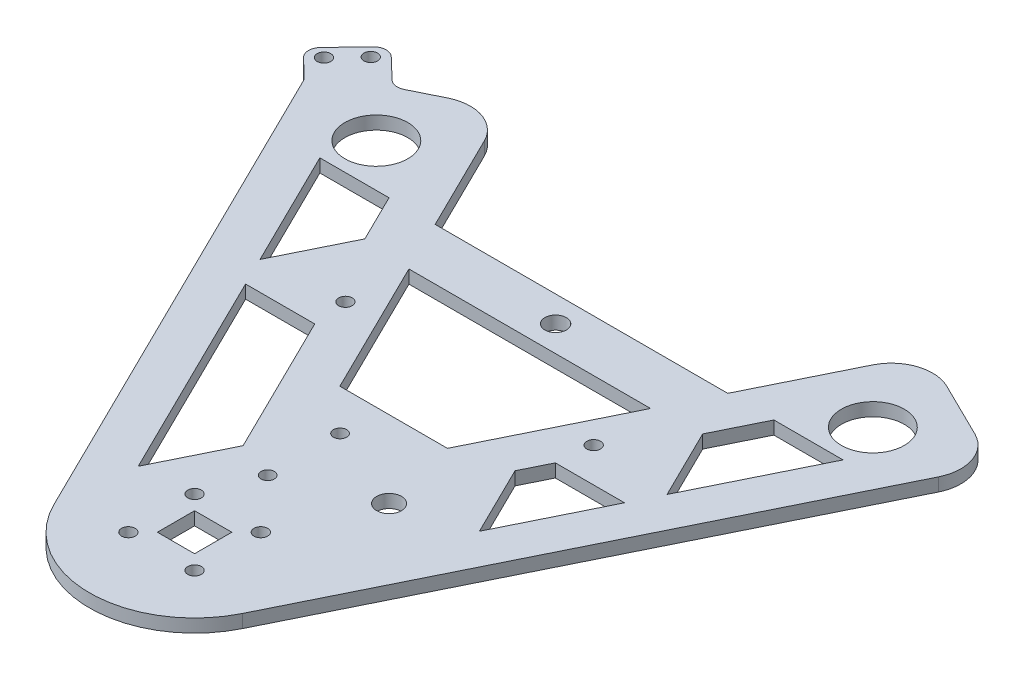
SolidWorks part; units mm, degrees
ref_plane "Front Plane" through (0, 0, 0) normal (0, 0, 1) x (1, 0, 0)
ref_plane "Top Plane" through (0, 0, 0) normal (0, 1, 0) x (1, 0, 0)
ref_plane "Right Plane" through (0, 0, 0) normal (1, 0, 0) x (0, 0, -1)
sketch "Sketch1" plane through (0, 0, 0) normal (0, 1, 0) x (1, 0, 0)
  line L0 (-60, 103.923) -> (60, 103.923) construction
  line L1 (-4.5, -4.5) -> (4.5, -4.5)
  line L2 (-4.5, -4.5) -> (-4.5, 4.5)
  line L3 (-4.5, 4.5) -> (4.5, 4.5)
  line L4 (4.5, -4.5) -> (4.5, 4.5)
  line L5 (-4.5, -4.5) -> (4.5, 4.5) construction
  line L6 (-4.5, 4.5) -> (4.5, -4.5) construction
  line L7 (-82.7138, 110.4306) -> (-22.7854, -11.2243)
  line L8 (22.7854, -11.2243) -> (82.7138, 110.4306)
  line L9 (-51.3166, 125.8972) -> (0, 21.7243)
  line L10 (0, 21.7243) -> (51.3166, 125.8972)
  line L11 (51.3166, 125.8972) -> (82.7138, 110.4306)
  line L12 (-82.7138, 110.4306) -> (-51.3166, 125.8972)
  line L13 (-57.5832, 99.017) -> (-36.1852, 55.5789) construction
  line L14 (-10.5973, -39.3898) -> (22084.5016, 44813.7774) construction
  line L15 (-13, 48.1143) -> (13, 48.1143)
  line L16 (17.5, 29.5105) -> (-3.1, 29.5105) construction
  line L17 (-8, -8) -> (8, -8) construction
  line L18 (-8, -8) -> (-8, 8) construction
  line L19 (-8, 8) -> (8, 8) construction
  line L20 (8, -8) -> (8, 8) construction
  line L21 (-8, -8) -> (8, 8) construction
  line L22 (-8, 8) -> (8, -8) construction
  line L23 (-3.1, 38.2605) -> (-3.1, 20.7605) construction
  line L24 (-30, 66.4531) -> (30, 66.4531) construction
  line L25 (-35.3574, 93.5) -> (35.3574, 93.5)
  line L26 (-29.1998, 81) -> (29.1998, 81)
  line L27 (0, 81) -> (0, 93.5) construction
  circle A0 centre (60, 103.923) radius 7.6
  circle A1 centre (-60, 103.923) radius 7.6
  arc A2 (22.7854, -11.2243) -> (-22.7854, -11.2243) centre (0, 0) cw
  circle A6 centre (-30, 66.4531) radius 1.65
  circle A7 centre (30, 66.4531) radius 1.65
  circle A8 centre (17.5, 29.5105) radius 3
  circle A9 centre (-8, 8) radius 1.65
  circle A10 centre (8, 8) radius 1.65
  circle A11 centre (8, -8) radius 1.65
  circle A12 centre (-8, -8) radius 1.65
  circle A13 centre (-3.1, 38.2605) radius 1.6
  circle A14 centre (-3.1, 20.7605) radius 1.6
  circle A15 centre (0, 87.25) radius 2.6
  point P4 (0, 0)
  point P10 (0, 103.923)
  point P19 (67.0152, 118.1639)
  point P20 (-67.0152, 118.1639)
  point P45 (0, 66.4531)
  point P49 (-3.1, 29.5105)
  point P56 (0, 87.25)
  dimension "D3" = 15.2
  dimension "D7" = 25.4
  dimension "D8" = 3.3
  dimension "D9" = 48
  dimension "D11" = 6
  dimension "D14" = 3.3
  dimension "D17" = 3.2
  dimension "D22" = 5.2
  dimension "D1" = 9
  dimension "D2" = 35
  dimension "D4" = 120
  dimension "D5" = 120
  dimension "D6" = 15.875
  dimension "D10" = 26
  dimension "D12" = 39
  dimension "D13" = 16
  dimension "D15" = 20.6
  dimension "D16" = 17.5
  dimension "D18" = 60
  dimension "D19" = 17.5
  dimension "D20" = 12.5
  dimension "D21" = 81
extrude "Boss-Extrude1" add sketch "Sketch1" along normal blind 3.175
fillet "Fillet1" radius 10 4 edges at (82.7138, 1.5875, -110.4306) (51.3166, 1.5875, -125.8972) (-51.3166, 1.5875, -125.8972) (-82.7138, 1.5875, -110.4306)
sketch "Sketch2" plane through (0, 3.175, 0) normal (0, 1, 0) x (1, 0, 0)
  line L0 (-45.7948, 58.1143) -> (-29.0736, 58.1143)
  line L1 (-29.0736, 58.1143) -> (-12.2548, 23.9721)
  line L2 (-12.2548, 23.9721) -> (-20.6154, 7)
  line L3 (-20.6154, 7) -> (-45.7948, 58.1143)
  line L8 (-63.2261, 93.5) -> (-49.1867, 65)
  line L9 (-49.1867, 65) -> (-40.8261, 81.9721)
  line L10 (-40.8261, 81.9721) -> (-46.5049, 93.5)
  line L11 (-46.5049, 93.5) -> (-63.2261, 93.5)
  line L12 (-78.2948, 101.46) -> (-22.7854, -11.2243) construction
  line L13 (-33.2051, 32.5572) -> (-42.1757, 28.1382) construction
  line L14 (-56.2064, 79.25) -> (-65.1771, 74.831) construction
  line L15 (-43.6655, 87.736) -> (-34.6949, 92.1551) construction
  line L16 (-20.6642, 41.0432) -> (-11.6935, 45.4622) construction
  line L17 (-29.1998, 81) -> (-13, 48.1143) construction
  line L18 (13, 48.1143) -> (29.1998, 81) construction
  line L19 (-29.1998, 81) -> (29.1998, 81) construction
  line L20 (-35.3574, 93.5) -> (35.3574, 93.5) construction
  line L21 (-13, 48.1143) -> (13, 48.1143) construction
  line L22 (29.0736, 58.1143) -> (45.7948, 58.1143)
  line L23 (45.7948, 58.1143) -> (34.2185, 34.6143)
  line L24 (34.2185, 34.6143) -> (25.8579, 51.5864)
  line L25 (25.8579, 51.5864) -> (29.0736, 58.1143)
  line L26 (46.5049, 93.5) -> (63.2261, 93.5)
  line L27 (63.2261, 93.5) -> (49.1867, 65)
  line L28 (49.1867, 65) -> (40.8261, 81.9721)
  line L29 (40.8261, 81.9721) -> (46.5049, 93.5)
  line L30 (22.7854, -11.2243) -> (78.2948, 101.46) construction
  line L31 (56.2064, 79.25) -> (65.1771, 74.831) construction
  line L32 (43.6655, 87.736) -> (34.6949, 92.1551) construction
  line L33 (35.3574, 93.5) -> (46.8976, 116.9266) construction
  dimension "D1" = 10
  dimension "D2" = 10
  dimension "D3" = 16
  dimension "D4" = 7
  dimension "D5" = 13.5
extrude "Cut-Extrude1" cut sketch "Sketch2" against normal through all both and the other way through all
sketch "Sketch3" plane through (0, 0, 0) normal (0, 1, 0) x (1, 0, 0)
  line L0 (-69.2579, 117.0592) -> (-77.9226, 125.3611)
  line L1 (-73.7432, 114.8497) -> (-60.2872, 121.4782) construction
  line L2 (-77.9226, 125.3611) -> (-88.3, 114.5301)
  line L3 (-88.3, 114.5301) -> (-81.545, 108.058)
  line L4 (-78.2948, 101.46) -> (-22.7854, -11.2243) construction
  line L5 (-83.7124, 114.9818) -> (-78.1778, 120.7584) construction
  line L6 (-83.1113, 119.9456) -> (-80.9451, 117.8701) construction
  line L7 (-81.545, 108.058) -> (-78.2948, 101.46)
  line L8 (-73.7432, 114.8497) -> (-69.2579, 117.0592)
  circle A0 centre (-78.1778, 120.7584) radius 1.65
  circle A1 centre (-83.7124, 114.9818) radius 1.65
  arc A2 (-78.2948, 101.46) -> (-73.7432, 114.8497) centre (-69.3241, 105.879) cw
  arc A3 (-73.7432, 114.8497) -> (-78.2948, 101.46) centre (-69.3241, 105.879) ccw construction
  dimension "D5" = 3.3
  dimension "D1" = 110
  dimension "D2" = 15
  dimension "D3" = 12
  dimension "D4" = 10
  dimension "D6" = 8
  dimension "D7" = 3
extrude "Boss-Extrude2" add sketch "Sketch3" along normal up to surface (3.175 mm away) up to face at (33.7362, 3.175, -50.6074)
fillet "Fillet2" radius 3 4 edges at (-88.3, 1.5875, -114.5301) (-77.9226, 1.5875, -125.3611) (-81.545, 1.5875, -108.058) (-69.2579, 1.5875, -117.0592)
